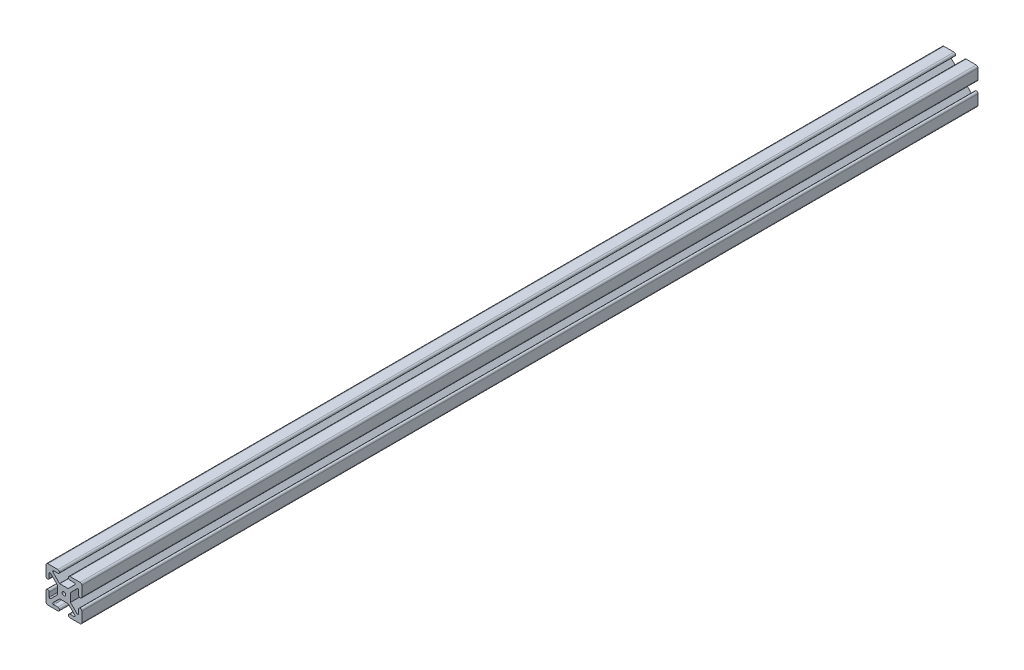
SolidWorks part; units mm, degrees
ref_plane "Front Plane" through (0, 0, 0) normal (0, 0, 1) x (1, 0, 0)
ref_plane "Top Plane" through (0, 0, 0) normal (0, 1, 0) x (1, 0, 0)
ref_plane "Right Plane" through (0, 0, 0) normal (1, 0, 0) x (0, 0, -1)
ref_plane "Plane1" through (0, 0, 50) normal (0, 0, 1) x (1, 0, 0)
sketch "Sketch1" plane through (0, 0, 50) normal (0, 0, 1) x (1, 0, 0)
  line L0 (-10, 9) -> (-10, 3.4)
  line L1 (-8.2, 3.4) -> (-8.2, 5.75)
  line L2 (-7.3464, 6.1036) -> (-3.656, 2.3842)
  line L3 (-3.65, 2.35) -> (-3.65, -2.35)
  line L4 (-3.656, -2.3842) -> (-7.3464, -6.1036)
  line L5 (-8.2, -5.75) -> (-8.2, -3.4)
  line L6 (-10, -3.4) -> (-10, -9)
  line L7 (-9, -10) -> (-3.4, -10)
  line L8 (-3.4, -8.2) -> (-5.75, -8.2)
  line L9 (-6.1036, -7.3464) -> (-2.444, -3.7158)
  line L10 (-2.35, -3.65) -> (2.35, -3.65)
  line L11 (2.444, -3.7158) -> (6.1036, -7.3464)
  line L12 (5.75, -8.2) -> (3.4, -8.2)
  line L13 (3.4, -10) -> (9, -10)
  line L14 (10, -9) -> (10, -3.4)
  line L15 (8.2, -3.4) -> (8.2, -5.75)
  line L16 (7.3464, -6.1036) -> (3.656, -2.3842)
  line L17 (3.65, -2.35) -> (3.65, 2.35)
  line L18 (3.656, 2.3842) -> (7.3464, 6.1036)
  line L19 (8.2, 5.75) -> (8.2, 3.4)
  line L20 (10, 3.4) -> (10, 9)
  line L21 (9, 10) -> (3.4, 10)
  line L22 (3.4, 8.2) -> (5.75, 8.2)
  line L23 (6.1036, 7.3464) -> (2.444, 3.7158)
  line L24 (2.35, 3.65) -> (-2.35, 3.65)
  line L25 (-2.444, 3.7158) -> (-6.1036, 7.3464)
  line L26 (-5.75, 8.2) -> (-3.4, 8.2)
  line L27 (-3.4, 10) -> (-9, 10)
  circle A0 centre (0, 0) radius 1
  arc A1 (-9, 10) -> (-10, 9) centre (-9, 9) ccw
  arc A2 (-10, 3.4) -> (-8.2, 3.4) centre (-9.1, 3.4) ccw
  arc A3 (-8.2, 5.75) -> (-7.3464, 6.1036) centre (-7.7, 5.75) cw
  arc A4 (-3.656, 2.3842) -> (-3.65, 2.35) centre (-3.75, 2.35) cw
  arc A5 (-3.65, -2.35) -> (-3.656, -2.3842) centre (-3.75, -2.35) cw
  arc A6 (-7.3464, -6.1036) -> (-8.2, -5.75) centre (-7.7, -5.75) cw
  arc A7 (-8.2, -3.4) -> (-10, -3.4) centre (-9.1, -3.4) ccw
  arc A8 (-10, -9) -> (-9, -10) centre (-9, -9) ccw
  arc A9 (-3.4, -10) -> (-3.4, -8.2) centre (-3.4, -9.1) ccw
  arc A10 (-5.75, -8.2) -> (-6.1036, -7.3464) centre (-5.75, -7.7) cw
  arc A11 (-2.444, -3.7158) -> (-2.35, -3.65) centre (-2.35, -3.75) cw
  arc A12 (2.35, -3.65) -> (2.444, -3.7158) centre (2.35, -3.75) cw
  arc A13 (6.1036, -7.3464) -> (5.75, -8.2) centre (5.75, -7.7) cw
  arc A14 (3.4, -8.2) -> (3.4, -10) centre (3.4, -9.1) ccw
  arc A15 (9, -10) -> (10, -9) centre (9, -9) ccw
  arc A16 (10, -3.4) -> (8.2, -3.4) centre (9.1, -3.4) ccw
  arc A17 (8.2, -5.75) -> (7.3464, -6.1036) centre (7.7, -5.75) cw
  arc A18 (3.656, -2.3842) -> (3.65, -2.35) centre (3.75, -2.35) cw
  arc A19 (3.65, 2.35) -> (3.656, 2.3842) centre (3.75, 2.35) cw
  arc A20 (7.3464, 6.1036) -> (8.2, 5.75) centre (7.7, 5.75) cw
  arc A21 (8.2, 3.4) -> (10, 3.4) centre (9.1, 3.4) ccw
  arc A22 (10, 9) -> (9, 10) centre (9, 9) ccw
  arc A23 (3.4, 10) -> (3.4, 8.2) centre (3.4, 9.1) ccw
  arc A24 (5.75, 8.2) -> (6.1036, 7.3464) centre (5.75, 7.7) cw
  arc A25 (2.444, 3.7158) -> (2.35, 3.65) centre (2.35, 3.75) cw
  arc A26 (-2.35, 3.65) -> (-2.444, 3.7158) centre (-2.35, 3.75) cw
  arc A27 (-6.1036, 7.3464) -> (-5.75, 8.2) centre (-5.75, 7.7) cw
  arc A28 (-3.4, 8.2) -> (-3.4, 10) centre (-3.4, 9.1) ccw
extrude "Boss-Extrude1" add sketch "Sketch1" against normal blind 500
